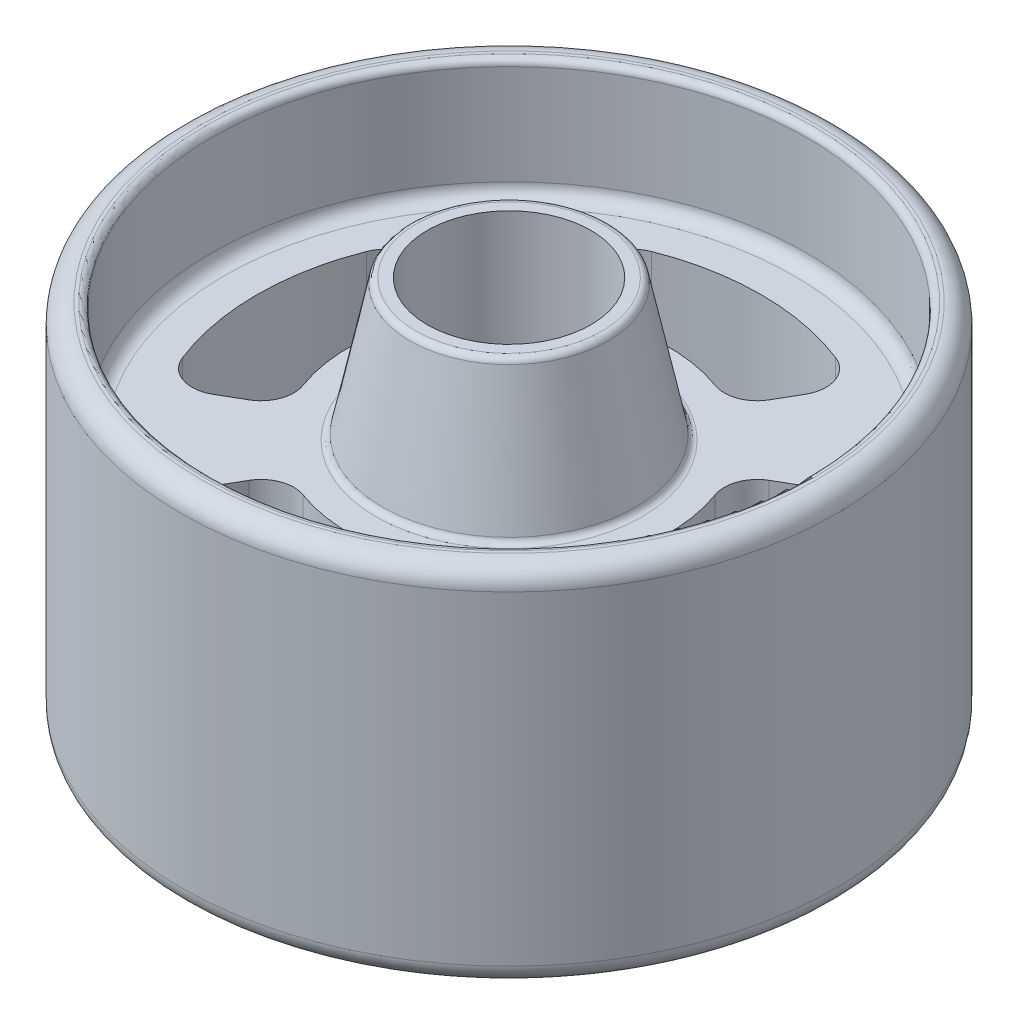
SolidWorks part; units mm, degrees
ref_plane "정면" through (0, 0, 0) normal (0, 0, 1) x (1, 0, 0)
ref_plane "윗면" through (0, 0, 0) normal (0, 1, 0) x (1, 0, 0)
ref_plane "우측면" through (0, 0, 0) normal (1, 0, 0) x (0, 0, -1)
sketch "스케치1" plane through (0, 0, 0) normal (0, 1, 0) x (1, 0, 0)
  circle A0 centre (0, 0) radius 50
  dimension "D1" = 100
extrude "보스-돌출1" add sketch "스케치1" along normal mid plane 9.5
sketch "스케치2" plane through (0, 0, 0) normal (0, 1, 0) x (1, 0, 0)
  line L0 (-14.5366, 25.1781) -> (-16.5624, 28.6869)
  line L1 (14.5366, 25.1781) -> (16.5624, 28.6869)
  line L2 (0, 0) -> (0, 95.6354) construction
  line L3 (0, 0) -> (50, 86.6025) construction
  line L4 (0, 0) -> (-50, 86.6025) construction
  line L5 (25.1781, 14.5366) -> (28.6869, 16.5624)
  line L6 (25.1781, -14.5366) -> (28.6869, -16.5624)
  line L7 (14.5366, -25.1781) -> (16.5624, -28.6869)
  line L8 (-14.5366, -25.1781) -> (-16.5624, -28.6869)
  line L9 (-25.1781, -14.5366) -> (-28.6869, -16.5624)
  line L10 (-25.1781, 14.5366) -> (-28.6869, 16.5624)
  arc A0 (8.4766, 22.9869) -> (-8.4766, 22.9869) centre (0, 0) ccw
  arc A1 (14.058, 35.8416) -> (-14.058, 35.8416) centre (0, 0) ccw
  arc A2 (-16.5624, 28.6869) -> (-14.058, 35.8416) centre (-12.2323, 31.1869) cw
  arc A3 (14.5366, 25.1781) -> (8.4766, 22.9869) centre (10.2065, 27.6781) cw
  arc A4 (-8.4766, 22.9869) -> (-14.5366, 25.1781) centre (-10.2065, 27.6781) cw
  arc A5 (16.5624, 28.6869) -> (14.058, 35.8416) centre (12.2323, 31.1869) ccw
  arc A6 (22.9869, -8.4766) -> (22.9869, 8.4766) centre (0, 0) ccw
  arc A7 (35.8416, -14.058) -> (35.8416, 14.058) centre (0, 0) ccw
  arc A8 (28.6869, 16.5624) -> (35.8416, 14.058) centre (31.1869, 12.2323) cw
  arc A9 (25.1781, -14.5366) -> (22.9869, -8.4766) centre (27.6781, -10.2065) cw
  arc A10 (22.9869, 8.4766) -> (25.1781, 14.5366) centre (27.6781, 10.2065) cw
  arc A11 (28.6869, -16.5624) -> (35.8416, -14.058) centre (31.1869, -12.2323) ccw
  arc A12 (-8.4766, -22.9869) -> (8.4766, -22.9869) centre (0, 0) ccw
  arc A13 (-14.058, -35.8416) -> (14.058, -35.8416) centre (0, 0) ccw
  arc A14 (16.5624, -28.6869) -> (14.058, -35.8416) centre (12.2323, -31.1869) cw
  arc A15 (-14.5366, -25.1781) -> (-8.4766, -22.9869) centre (-10.2065, -27.6781) cw
  arc A16 (8.4766, -22.9869) -> (14.5366, -25.1781) centre (10.2065, -27.6781) cw
  arc A17 (-16.5624, -28.6869) -> (-14.058, -35.8416) centre (-12.2323, -31.1869) ccw
  arc A18 (-22.9869, 8.4766) -> (-22.9869, -8.4766) centre (0, 0) ccw
  arc A19 (-35.8416, 14.058) -> (-35.8416, -14.058) centre (0, 0) ccw
  arc A20 (-28.6869, -16.5624) -> (-35.8416, -14.058) centre (-31.1869, -12.2323) cw
  arc A21 (-25.1781, 14.5366) -> (-22.9869, 8.4766) centre (-27.6781, 10.2065) cw
  arc A22 (-22.9869, -8.4766) -> (-25.1781, -14.5366) centre (-27.6781, -10.2065) cw
  arc A23 (-28.6869, 16.5624) -> (-35.8416, 14.058) centre (-31.1869, 12.2323) ccw
  circle A24 centre (0, 0) radius 12.5
  point P56 (0, 0)
  dimension "D1" = 49
  dimension "D2" = 77
  dimension "D3" = 5
  dimension "D7" = 25
  dimension "D4" = 4
  dimension "D5" = 60
  dimension "D6" = 30
extrude "컷-돌출1" cut sketch "스케치2" against normal through all both and the other way through all
sketch "스케치4" plane through (0, 0, 0) normal (0, 0, 1) x (1, 0, 0)
  line L0 (12.5, 31) -> (14.1876, 31)
  line L1 (15.1664, 30.2049) -> (19.5, 9.5)
  line L2 (19.5, 9.5) -> (43.5, 9.5)
  line L3 (45.5, 11.5) -> (45.5, 26.75)
  line L4 (46.5, 27.75) -> (47, 27.75)
  line L5 (50, 24.75) -> (50, 4.75)
  line L6 (50, 4.75) -> (12.5, 4.75)
  line L7 (14.058, 4.75) -> (-14.058, 4.75) construction
  line L8 (12.5, 4.75) -> (12.5, 31)
  arc A0 (50, 24.75) -> (47, 27.75) centre (47, 24.75) ccw
  arc A1 (45.5, 11.5) -> (43.5, 9.5) centre (43.5, 11.5) cw
  arc A2 (45.5, 26.75) -> (46.5, 27.75) centre (46.5, 26.75) cw
  arc A3 (15.1664, 30.2049) -> (14.1876, 31) centre (14.1876, 30) ccw
  point P2 (45.6102, 27.75)
  point P12 (45.5, 19.125)
  point P16 (50, 27.75)
  point P19 (45.5, 9.5)
  point P22 (45.5, 27.75)
  point P25 (15, 31)
  dimension "D9" = 3
  dimension "D10" = 2
  dimension "D11" = 1
  dimension "D12" = 1
  dimension "D1" = 23
  dimension "D2" = 31
  dimension "D3" = 50
  dimension "D4" = 30.5
  dimension "D5" = 26
  dimension "D6" = 12.5
  dimension "D7" = 4.75
  dimension "D8" = 45.5
ref_axis "기준축1" through (0, 4.75, 0) along (0, -1, 0)
revolve "회전1" add sketch "스케치4" angle 360 about axis through (0, 4.75, 0) along (0, -1, 0)
mirror "대칭 복사1" about plane through (0, 0, 0) normal (0, 1, 0) of "회전1"
sketch "스케치9" plane through (0, 0, 0) normal (0, 1, 0) x (1, 0, 0)
  line L0 (-14.5366, 25.1781) -> (-16.5624, 28.6869)
  line L1 (14.5366, 25.1781) -> (16.5624, 28.6869)
  line L2 (0, 0) -> (0, 95.6354) construction
  line L3 (0, 0) -> (50, 86.6025) construction
  line L4 (0, 0) -> (-50, 86.6025) construction
  line L5 (25.1781, 14.5366) -> (28.6869, 16.5624)
  line L6 (25.1781, -14.5366) -> (28.6869, -16.5624)
  line L7 (14.5366, -25.1781) -> (16.5624, -28.6869)
  line L8 (-14.5366, -25.1781) -> (-16.5624, -28.6869)
  line L9 (-25.1781, -14.5366) -> (-28.6869, -16.5624)
  line L10 (-25.1781, 14.5366) -> (-28.6869, 16.5624)
  arc A0 (8.4766, 22.9869) -> (-8.4766, 22.9869) centre (0, 0) ccw
  arc A1 (14.058, 35.8416) -> (-14.058, 35.8416) centre (0, 0) ccw
  arc A2 (-16.5624, 28.6869) -> (-14.058, 35.8416) centre (-12.2323, 31.1869) cw
  arc A3 (14.5366, 25.1781) -> (8.4766, 22.9869) centre (10.2065, 27.6781) cw
  arc A4 (-8.4766, 22.9869) -> (-14.5366, 25.1781) centre (-10.2065, 27.6781) cw
  arc A5 (16.5624, 28.6869) -> (14.058, 35.8416) centre (12.2323, 31.1869) ccw
  arc A6 (22.9869, -8.4766) -> (22.9869, 8.4766) centre (0, 0) ccw
  arc A7 (35.8416, -14.058) -> (35.8416, 14.058) centre (0, 0) ccw
  arc A8 (28.6869, 16.5624) -> (35.8416, 14.058) centre (31.1869, 12.2323) cw
  arc A9 (25.1781, -14.5366) -> (22.9869, -8.4766) centre (27.6781, -10.2065) cw
  arc A10 (22.9869, 8.4766) -> (25.1781, 14.5366) centre (27.6781, 10.2065) cw
  arc A11 (28.6869, -16.5624) -> (35.8416, -14.058) centre (31.1869, -12.2323) ccw
  arc A12 (-8.4766, -22.9869) -> (8.4766, -22.9869) centre (0, 0) ccw
  arc A13 (-14.058, -35.8416) -> (14.058, -35.8416) centre (0, 0) ccw
  arc A14 (16.5624, -28.6869) -> (14.058, -35.8416) centre (12.2323, -31.1869) cw
  arc A15 (-14.5366, -25.1781) -> (-8.4766, -22.9869) centre (-10.2065, -27.6781) cw
  arc A16 (8.4766, -22.9869) -> (14.5366, -25.1781) centre (10.2065, -27.6781) cw
  arc A17 (-16.5624, -28.6869) -> (-14.058, -35.8416) centre (-12.2323, -31.1869) ccw
  arc A18 (-22.9869, 8.4766) -> (-22.9869, -8.4766) centre (0, 0) ccw
  arc A19 (-35.8416, 14.058) -> (-35.8416, -14.058) centre (0, 0) ccw
  arc A20 (-28.6869, -16.5624) -> (-35.8416, -14.058) centre (-31.1869, -12.2323) cw
  arc A21 (-25.1781, 14.5366) -> (-22.9869, 8.4766) centre (-27.6781, 10.2065) cw
  arc A22 (-22.9869, -8.4766) -> (-25.1781, -14.5366) centre (-27.6781, -10.2065) cw
  arc A23 (-28.6869, 16.5624) -> (-35.8416, 14.058) centre (-31.1869, 12.2323) ccw
  circle A24 centre (0, 0) radius 12.5
  point P56 (0, 0)
  dimension "D1" = 49
  dimension "D2" = 77
  dimension "D3" = 5
  dimension "D7" = 25
  dimension "D4" = 4
  dimension "D5" = 60
  dimension "D6" = 30
extrude "컷-돌출2" cut sketch "스케치9" against normal through all both and the other way through all
fillet "필렛1" radius 1 2 edges at (0, -9.5, 19.5) (0, 9.5, 19.5)
